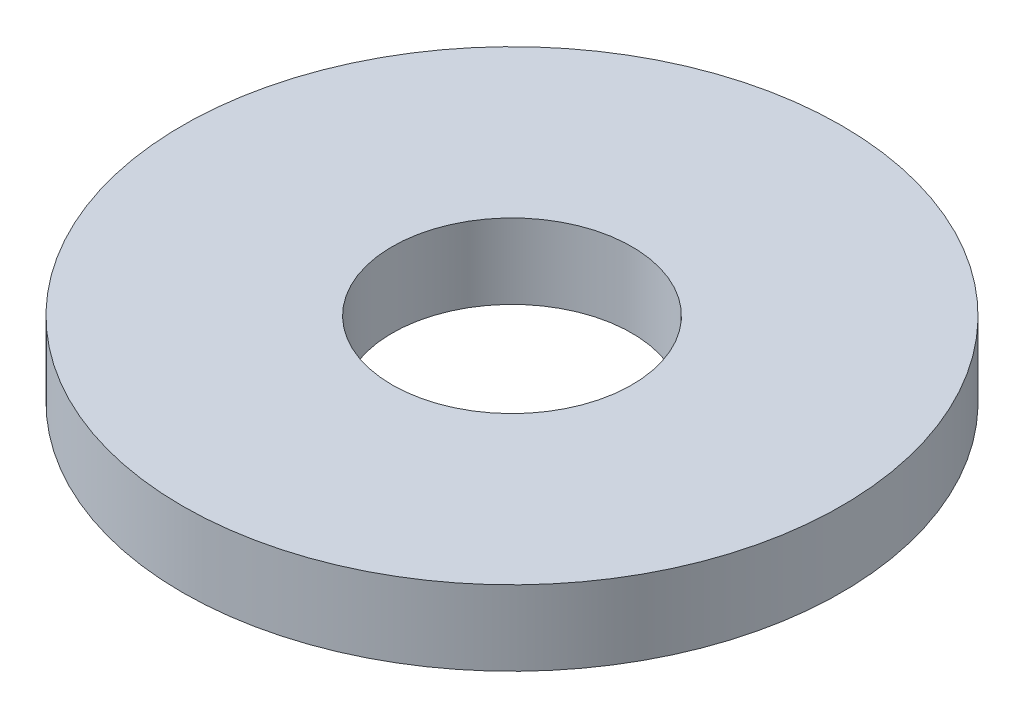
SolidWorks part; units mm, degrees
material "1023 Carbon Steel Sheet (SS)"
ref_plane "Front Plane" through (0, 0, 0) normal (0, 0, 1) x (1, 0, 0)
ref_plane "Top Plane" through (0, 0, 0) normal (0, 1, 0) x (1, 0, 0)
ref_plane "Right Plane" through (0, 0, 0) normal (1, 0, 0) x (0, 0, -1)
sketch "Sketch1" plane through (0, 0, 0) normal (0, 1, 0) x (1, 0, 0)
  circle A0 centre (0, 0) radius 8.7312
  circle A1 centre (0, 0) radius 3.175
  dimension "D1" = 6.35
  dimension "D2" = 17.4625
extrude "Boss-Extrude1" add sketch "Sketch1" along normal blind 1.9844
